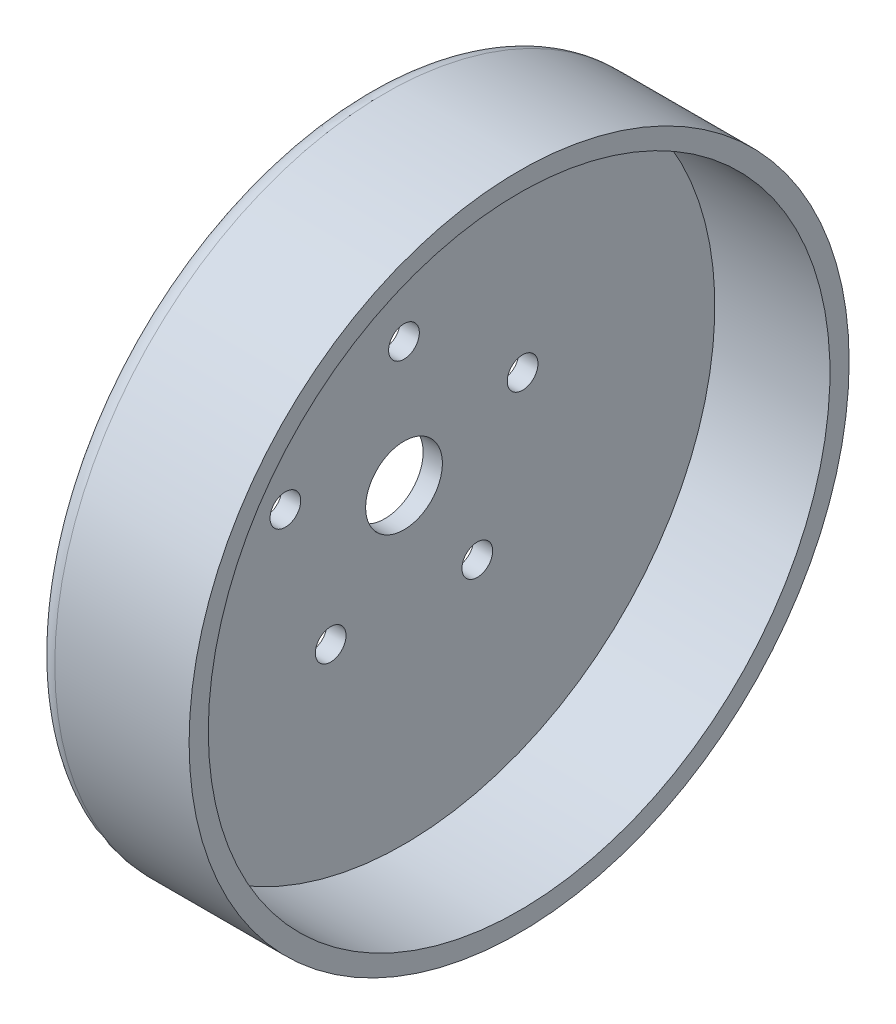
SolidWorks part; units mm, degrees
ref_plane "Front Plane" through (0, 0, 0) normal (0, 0, 1) x (1, 0, 0)
ref_plane "Top Plane" through (0, 0, 0) normal (0, 1, 0) x (1, 0, 0)
ref_plane "Right Plane" through (0, 0, 0) normal (1, 0, 0) x (0, 0, -1)
sketch "Sketch1" plane through (0, 0, 0) normal (0, 0, 1) x (1, 0, 0)
  line L0 (0, 0) -> (0, 81)
  line L1 (0, 81) -> (30, 81)
  line L2 (30, 81) -> (30, 86)
  line L3 (30, 86) -> (-10, 86)
  line L4 (-10, 86) -> (-10, 0)
  line L5 (-10, 0) -> (0, 0)
  dimension "D1" = 81
  dimension "D2" = 30
  dimension "D3" = 10
  dimension "D4" = 5
revolve "Revolve1" add sketch "Sketch1" angle 360 about L5
fillet "Fillet1" radius 5 1 edges at (-10, 0, 86)
sketch "Sketch2" plane through (-10, 0, 0) normal (-1, 0, 0) x (0, 0, 1)
  circle A0 centre (0, 0) radius 45
  dimension "D1" = 90
extrude "Cut-Extrude1" cut sketch "Sketch2" against normal blind 5
sketch "Sketch3" plane through (-10, 0, 0) normal (-1, 0, 0) x (0, 0, 1)
  circle A0 centre (0, 0) radius 10
  dimension "D1" = 20
extrude "Cut-Extrude2" cut sketch "Sketch3" against normal through all
sketch "Sketch4" plane through (-5, 0, 0) normal (-1, 0, 0) x (0, 0, 1)
  circle A0 centre (0, 0) radius 32.5 construction
  circle A1 centre (0, 32.5) radius 4
  circle A2 centre (30.9093, 10.0431) radius 4
  circle A3 centre (19.103, -26.2931) radius 4
  circle A4 centre (-19.103, -26.2931) radius 4
  circle A5 centre (-30.9093, 10.0431) radius 4
  point P15 (0, 0)
  dimension "D1" = 65
  dimension "D2" = 8
  dimension "D3" = 5
extrude "Cut-Extrude3" cut sketch "Sketch4" against normal up to next contours A4 | A3 | A2 | A1 | A5
